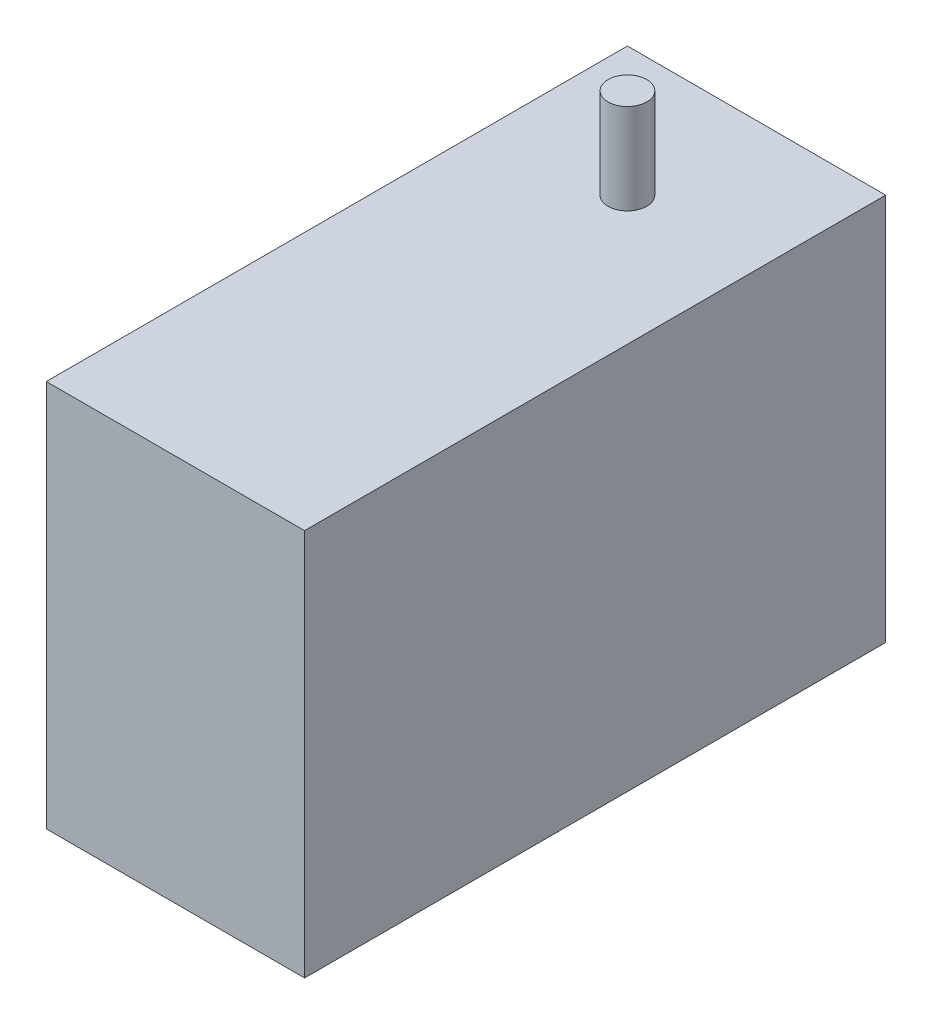
SolidWorks part; units mm, degrees
ref_plane "Ön Düzlem" through (0, 0, 0) normal (0, 0, 1) x (1, 0, 0)
ref_plane "Üst Düzlem" through (0, 0, 0) normal (0, 1, 0) x (1, 0, 0)
ref_plane "Sağ Düzlem" through (0, 0, 0) normal (1, 0, 0) x (0, 0, -1)
sketch "Sketch1" plane through (0, 0, 0) normal (0, 1, 0) x (1, 0, 0)
  line L1 (-10, 22.5) -> (10, 22.5)
  line L2 (-10, 22.5) -> (-10, -22.5)
  line L3 (-10, -22.5) -> (10, -22.5)
  line L4 (10, 22.5) -> (10, -22.5)
  line L5 (-10, 22.5) -> (10, -22.5) construction
  line L6 (-10, -22.5) -> (10, 22.5) construction
  point P0 (0, 0)
  dimension "D1" = 45
  dimension "D2" = 20
extrude "Boss-Extrude1" add sketch "Sketch1" along normal blind 30
sketch "Sketch2" plane through (0, 30, 0) normal (0, 1, 0) x (1, 0, 0)
  line L2 (10, 22.5) -> (-10, 22.5) construction
  circle A0 centre (0, 12.5) radius 1.5
  dimension "D1" = 10
  dimension "D2" = 3
extrude "Boss-Extrude2" add sketch "Sketch2" along normal blind 7
hole_wizard "#4-48 Tapped Hole1" positions "Sketch4" profile "Sketch3" tap size "#4-48" standard "ANSI Inch"
sketch "Sketch4" plane through (-10, 0, 0) normal (-1, 0, 0) x (0, 0, 1)
  point P0 (-12.8, 7.5)
  point P3 (-12.8, 22.5)
  point P6 (14.5, 22.5)
  point P9 (14.5, 7.5)
sketch "Sketch3" plane through (-10, 7.5, -12.8) normal (0, 1, 0) x (0, 0, 1)
  line L0 (0, 0) -> (0, 4.2135)
  line L1 (0, 4.2135) -> (1.1874, 3.5)
  line L2 (1.1874, 3.5) -> (1.1874, 0)
  line L5 (1.1874, 0) -> (0, 0)
  line L10 (0, 4.2135) -> (-1.1875, 3.5) construction
  line L11 (0, -6.35) -> (0, 107.95) construction
  dimension "Tap Drill Dia." = 2.3749
  dimension "Tap Drill Depth" = 3.5
  dimension "Drill Angle" = 118
